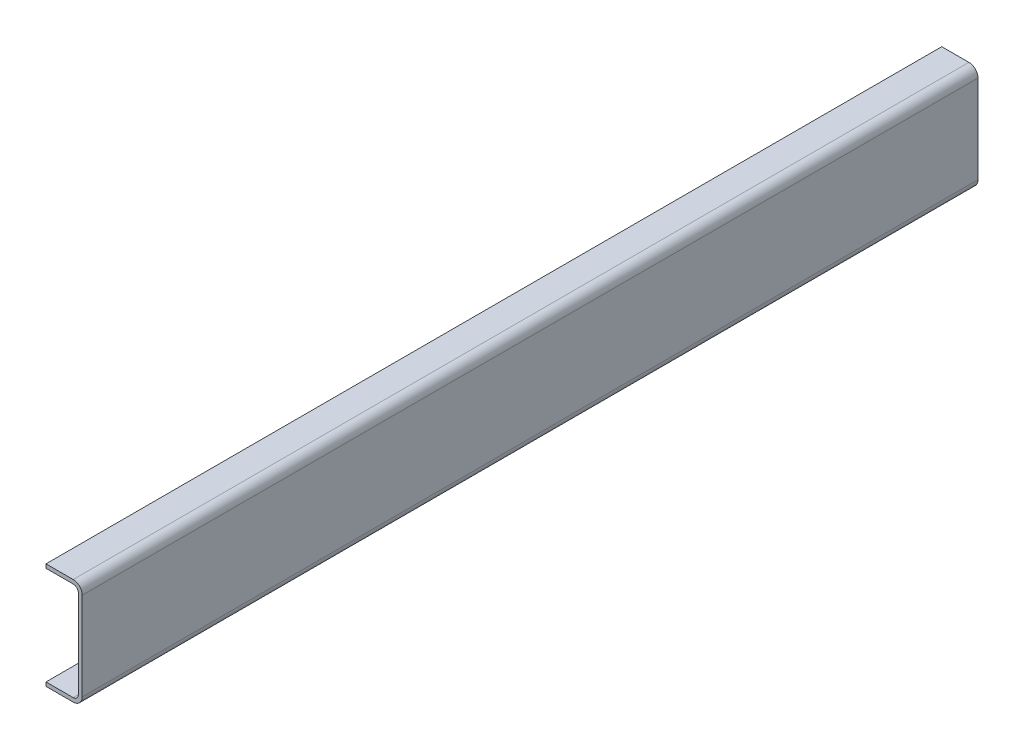
SolidWorks part; units mm, degrees
material "ASTM A572, GR50"
ref_plane "Edge of Rail 1" through (0, 0, 0) normal (0, 0, 1) x (1, 0, 0)
ref_plane "Bottom Flange" through (0, 0, 0) normal (0, 1, 0) x (1, 0, 0)
ref_plane "Outside Web" through (0, 0, 0) normal (1, 0, 0) x (0, 0, -1)
ref_plane "Top Flange" through (0, 260.35, 0) normal (0, 1, 0) x (-1, 0, 0)
ref_plane "Edge of Rail 2" through (0, 0, -2197.1) normal (0, 0, 1) x (1, 0, 0)
ref_plane "Inside Flange Edge" through (-88.9, 0, 0) normal (1, 0, 0) x (0, 0, -1)
sketch "Sketch1" plane through (0, 0, 0) normal (0, 0, 1) x (1, 0, 0)
  line L1 (-88.9, 0) -> (0, 0)
  line L2 (-88.9, -50) -> (-88.9, 50) construction
  line L3 (-88.9, 260.35) -> (0, 260.35)
  line L4 (0, 0) -> (0, 260.35)
  dimension "D1" = 260.35
extrude "Base-Extrude-Thin" add sketch "Sketch1" against normal up to surface (2197.1 mm away) thin up to plane "Edge of Rail 2" thin type one direction wall 9.525
fillet "Inside Bend Radius" radius 12.7 2 edges at (-9.525, 250.825, -1098.55) (-9.525, 9.525, -1098.55)
fillet "Outside Bend Radius" radius 22.225 2 edges at (0, 0, -1098.55) (0, 260.35, -1098.55)
equation "\"OUTSIDE_RADIUS@Outside Bend Radius\" = \"INSIDE_RADIUS@Inside Bend Radius\"+\"THICKNESS@Base-Extrude-Thin\""
